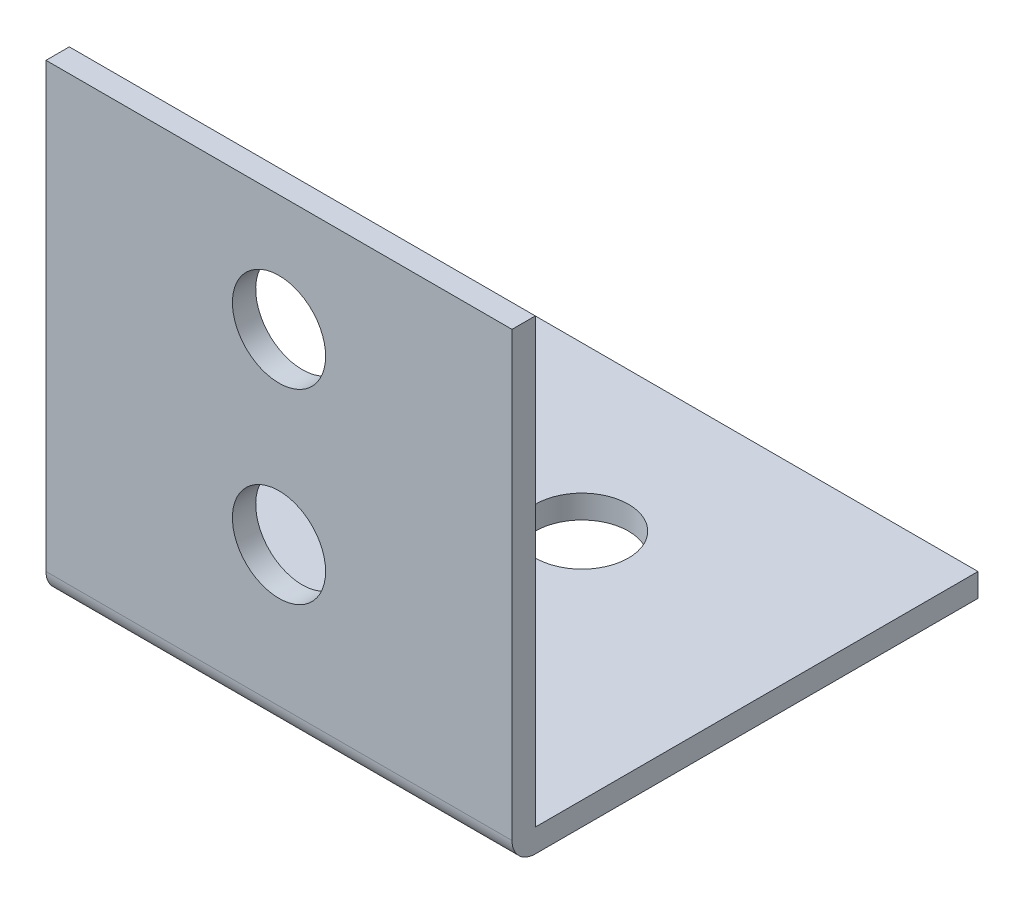
SolidWorks part; units mm, degrees
ref_plane "Front Plane" through (0, 0, 0) normal (0, 0, 1) x (1, 0, 0)
ref_plane "Top Plane" through (0, 0, 0) normal (0, 1, 0) x (1, 0, 0)
ref_plane "Right Plane" through (0, 0, 0) normal (1, 0, 0) x (0, 0, -1)
sketch "Sketch1" plane through (0, 0, 0) normal (1, 0, 0) x (0, 0, -1)
  line L0 (20, 0) -> (1, 0)
  line L1 (0, 1) -> (0, 20)
  line L2 (20, 1) -> (1, 1)
  line L3 (1, 1) -> (1, 20)
  line L4 (0, 20) -> (1, 20)
  line L5 (20, 1) -> (20, 0)
  arc A0 (1, 0) -> (0, 1) centre (1, 1) cw
  arc A1 (1, 1) -> (1, 1) centre (1, 1) cw
  point P6 (0, 0)
  dimension "D3" = 1
  dimension "D1" = 20
  dimension "D2" = 20
  dimension "D4" = 1
extrude "Boss-Extrude1" add sketch "Sketch1" along normal mid plane 20
sketch "Sketch2" plane through (0, 0, 0) normal (0, 0, 1) x (1, 0, 0)
  line L0 (10, 0) -> (-10, 0) construction
  circle A0 centre (0, 7) radius 2
  circle A1 centre (0, 15) radius 2
  dimension "D1" = 4
  dimension "D2" = 8
  dimension "D3" = 7
extrude "Cut-Extrude1" cut sketch "Sketch2" against normal blind 20
sketch "Sketch3" plane through (0, 0, 0) normal (0, -1, 0) x (1, 0, 0)
  line L0 (10, 0) -> (-10, 0) construction
  circle A0 centre (0, -13) radius 2
  circle A1 centre (0, -5) radius 2
  dimension "D1" = 4
  dimension "D2" = 8
  dimension "D3" = 5
extrude "Cut-Extrude2" cut sketch "Sketch3" against normal blind 20
